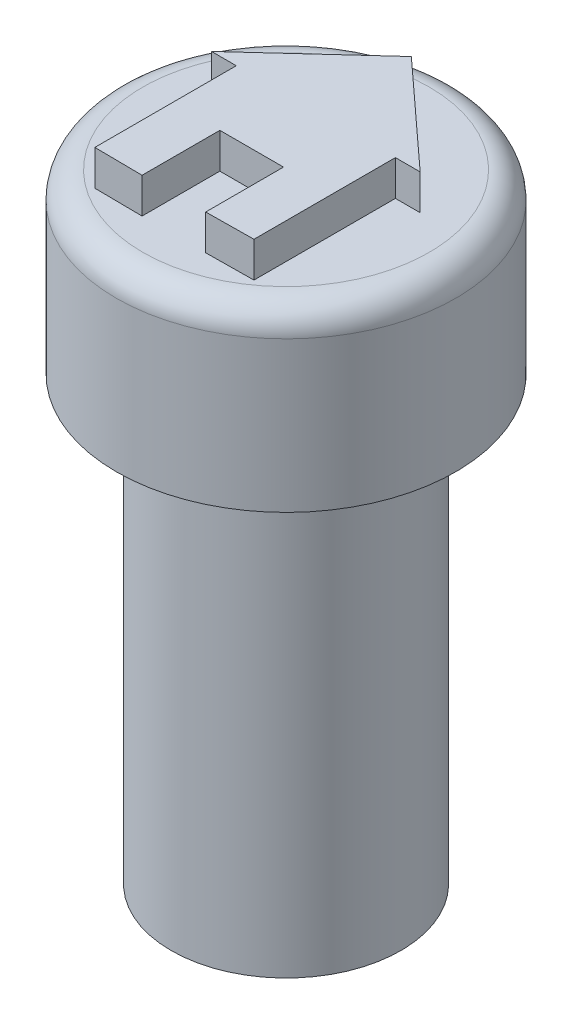
SolidWorks part; units mm, degrees
ref_plane "Front Plane" through (0, 0, 0) normal (0, 0, 1) x (1, 0, 0)
ref_plane "Top Plane" through (0, 0, 0) normal (0, 1, 0) x (1, 0, 0)
ref_plane "Right Plane" through (0, 0, 0) normal (1, 0, 0) x (0, 0, -1)
sketch "Sketch1" plane through (0, 0, 0) normal (0, 1, 0) x (1, 0, 0)
  circle A0 centre (0, 0) radius 3.25
  dimension "D1" = 6.5
extrude "Boss-Extrude1" add sketch "Sketch1" along normal blind 12.5 contours A0
sketch "Sketch2" plane through (0, 0, 0) normal (0, -1, 0) x (1, 0, 0)
  circle A1 centre (0, 0) radius 1.75
  dimension "D1" = 3.5
extrude "Cut-Extrude1" cut sketch "Sketch2" against normal blind 2.5
sketch "Sketch6" plane through (0, 12.5, 0) normal (0, 1, 0) x (1, 0, 0)
  circle A0 centre (0, 0) radius 4.8
  dimension "D1" = 9.6
extrude "Boss-Extrude2" add sketch "Sketch6" along normal blind 5 contours A0
sketch "Sketch7" plane through (0, 17.5, 0) normal (0, 1, 0) x (1, 0, 0)
  line L0 (-2.25, 0) -> (2.25, 0) construction
  line L1 (-2.25, 2.25) -> (2.25, 2.25)
  line L2 (-2.25, 2.25) -> (-2.25, -2.25)
  line L3 (-2.25, -2.25) -> (2.25, -2.25)
  line L4 (2.25, 2.25) -> (2.25, -2.25)
  line L5 (-2.25, 2.25) -> (2.25, -2.25) construction
  line L6 (-2.25, -2.25) -> (2.25, 2.25) construction
  line L7 (-2.25, 2.25) -> (-2.25, -2.25)
  line L8 (0, 0) -> (0, 2.25) construction
  dimension "D1" = 4.5
  dimension "D2" = 4.5
  dimension "D3" = 2.25
sketch "Sketch9" plane through (0, 17.5, 0) normal (0, 1, 0) x (1, 0, 0)
  line L0 (0, 0.8425) -> (0, 3.5425) construction
  line L1 (-2.25, 0.8425) -> (2.25, 0.8425)
  line L2 (-2.25, 0.8425) -> (-2.25, -3.1575)
  line L3 (-2.25, -3.1575) -> (2.25, -3.1575)
  line L4 (2.25, 0.8425) -> (2.25, -3.1575)
  line L7 (-2.95, 0.8425) -> (0, 3.5425)
  line L8 (2.25, 0.8425) -> (2.95, 0.8425)
  line L9 (-2.25, 0.8425) -> (-2.95, 0.8425)
  line L10 (0, 3.5425) -> (2.95, 0.8425)
  line L12 (-0.9, -3.1724) -> (0.9, -3.1724)
  line L13 (-0.9, -3.1724) -> (-0.9, -0.9724)
  line L14 (-0.9, -0.9724) -> (0.9, -0.9724)
  line L15 (0.9, -3.1724) -> (0.9, -0.9724)
  line L19 (0, -0.9724) -> (0, 0.8425) construction
  dimension "D1" = 4
  dimension "D2" = 4.5
  dimension "D3" = 2.7
  dimension "D4" = 0.7
  dimension "D5" = 0.7
  dimension "D6" = 2.2
  dimension "D7" = 1.8
  dimension "D8" = 0.9
  dimension "D12" = 0.8425
  dimension "D13" = 0.9724
sketch "Sketch12" plane through (0, 17.5, 0) normal (0, 1, 0) x (1, 0, 0)
  line L0 (0, 3.5425) -> (-2.95, 0.8425)
  line L1 (-2.95, 0.8425) -> (-2.25, 0.8425)
  line L2 (-2.25, 0.8425) -> (-2.25, -3.1575)
  line L3 (-2.25, -3.1575) -> (-0.9, -3.1724)
  line L4 (-0.9, -3.1724) -> (-0.9, -0.9724)
  line L5 (-0.9, -0.9724) -> (0.9, -0.9724)
  line L6 (0.9, -0.9724) -> (0.9, -3.1724)
  line L7 (0.9, -3.1724) -> (2.25, -3.1575)
  line L8 (2.25, -3.1575) -> (2.25, 0.8425)
  line L9 (2.25, 0.8425) -> (2.95, 0.8425)
  line L10 (2.95, 0.8425) -> (0, 3.5425)
extrude "Boss-Extrude3" add sketch "Sketch12" along normal blind 1
fillet "Fillet1" radius 0.75 1 edges at (0, 17.5, 4.8)
